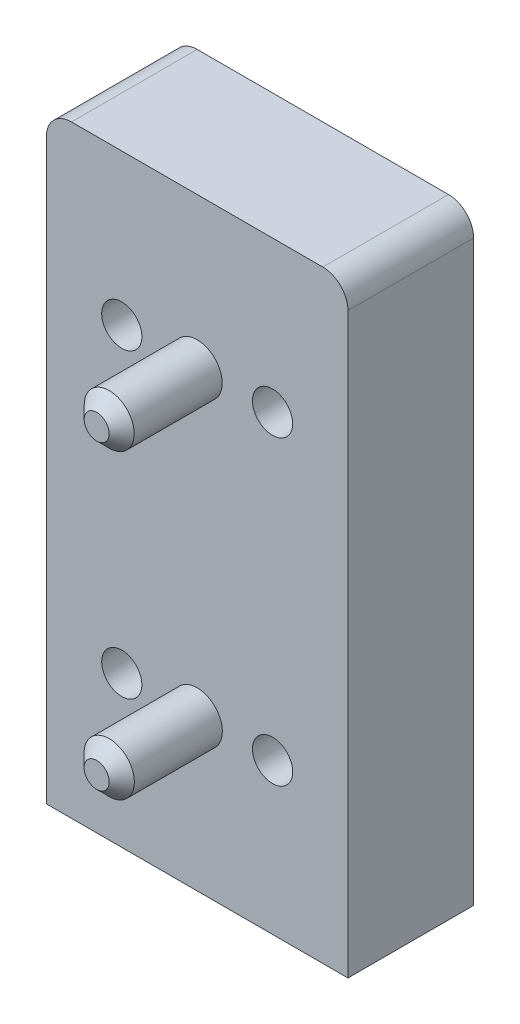
SolidWorks part; units mm, degrees
material "6061 Сплав"
ref_plane "Спереди" through (0, 0, 0) normal (0, 0, 1) x (1, 0, 0)
ref_plane "Сверху" through (0, 0, 0) normal (0, 1, 0) x (1, 0, 0)
ref_plane "Справа" through (0, 0, 0) normal (1, 0, 0) x (0, 0, -1)
sketch "Sketch1" plane through (0, 0, 0) normal (0, 0, 1) x (1, 0, 0)
  line L1 (-12, -36) -> (12, -36)
  line L2 (-12, -36) -> (-12, 10)
  line L3 (-10, 12) -> (10, 12)
  line L4 (12, -36) -> (12, 10)
  arc A0 (-12, 10) -> (-10, 12) centre (-10, 10) cw
  arc A1 (10, 12) -> (12, 10) centre (10, 10) cw
  point P0 (0, 0)
  point P10 (12, 12)
  dimension "D1" = 2
extrude "Boss-Extrude1" add sketch "Sketch1" along normal blind 10
sketch "Sketch2" plane through (0, 0, 0) normal (0, 0, -1) x (-1, 0, 0)
  line L0 (-1, -1.5) -> (1, -1.5)
  line L1 (-1.5, -1) -> (-1.5, 1)
  line L2 (-1, 1.5) -> (1, 1.5)
  line L3 (1.5, -1) -> (1.5, 1)
  line L4 (-1.5, -1.5) -> (1.5, 1.5) construction
  line L5 (-1.5, 1.5) -> (1.5, -1.5) construction
  line L6 (-1.76, -26.26) -> (1.76, -26.26)
  line L7 (-2.26, -25.76) -> (-2.26, -22.24)
  line L8 (-1.76, -21.74) -> (1.76, -21.74)
  line L9 (2.26, -25.76) -> (2.26, -22.24)
  line L10 (-2.26, -26.26) -> (2.26, -21.74) construction
  line L11 (-2.26, -21.74) -> (2.26, -26.26) construction
  circle A0 centre (4, -8) radius 1
  arc A1 (1.5, 1) -> (1, 1.5) centre (1.5, 1.5) ccw
  arc A2 (-1, 1.5) -> (-1.5, 1) centre (-1.5, 1.5) ccw
  arc A3 (1, -1.5) -> (1.5, -1) centre (1.5, -1.5) ccw
  arc A4 (-1.5, -1) -> (-1, -1.5) centre (-1.5, -1.5) ccw
  circle A5 centre (-0.116, -14.973) radius 1
  arc A6 (2.26, -22.24) -> (1.76, -21.74) centre (2.26, -21.74) ccw
  arc A7 (-1.76, -21.74) -> (-2.26, -22.24) centre (-2.26, -21.74) ccw
  arc A8 (-2.26, -25.76) -> (-1.76, -26.26) centre (-2.26, -26.26) ccw
  arc A9 (1.76, -26.26) -> (2.26, -25.76) centre (2.26, -26.26) ccw
  point P0 (0, 0)
  point P1 (0, 0)
  point P6 (-0.5312, 0.5468)
  point P7 (-0.5312, 0.5468)
  point P10 (7.5, 9)
  point P11 (-6.5, -8)
  point P12 (-6.5, 9)
  point P13 (7.5, -8)
  point P27 (0, -24)
  point P28 (0, -24)
  point P34 (6.884, -14.975)
  point P35 (-7.116, -14.973)
  point P36 (-7.116, -31.973)
  point P37 (6.884, -31.973)
  dimension "D11" = 3
  dimension "D24" = 0.5
  dimension "D1" = 9
  dimension "D2" = 8
  dimension "D3" = 6.5
  dimension "D4" = 7.5
  dimension "D5" = 8
  dimension "D6" = 9
  dimension "D7" = 6.5
  dimension "D8" = 7.5
  dimension "D9" = 3.5
  dimension "D10" = 8
  dimension "D12" = 3
  dimension "D13" = 7.116
  dimension "D14" = 6.884
  dimension "D15" = 9.025
  dimension "D16" = 7.973
  dimension "D17" = 6.884
  dimension "D18" = 7.116
  dimension "D19" = 7.973
  dimension "D20" = 9.027
  dimension "D21" = 7
  dimension "D22" = 4.52
  dimension "D23" = 4.52
  dimension "D25" = 9.027
extrude "Cut-Extrude1" cut sketch "Sketch2" against normal blind 0.6
sketch "Sketch3" plane through (0, 0, 10) normal (0, 0, 1) x (1, 0, 0)
  circle A0 centre (0, 0) radius 1.99
  circle A1 centre (0, -24) radius 2
extrude "Boss-Extrude3" add sketch "Sketch3" along normal blind 8
sketch "Sketch6" plane through (0, 0, 0) normal (0, 0, -1) x (-1, 0, 0)
  point P0 (6, 0)
  point P1 (-6, 0)
chamfer "Chamfer3" distance 1 angle 45 2 edges at (1.99, 0, 18) (2, -24, 18)
hole_wizard "Зенковка для  винта с полупотайной головкой M31" positions "Sketch11" profile "Sketch12" countersink size "M3" standard "Ansi Metric" end condition through all
sketch "Sketch11" plane through (0, 0, 0) normal (0, 0, -1) x (-1, 0, 0)
  point P0 (6, 0)
  point P3 (-6, 0)
  point P6 (-6, -24)
  point P8 (6, -24)
sketch "Sketch12" plane through (-6, 0, 0) normal (1, 0, 0) x (0, 1, 0)
  line L0 (0, 0) -> (0, 18)
  line L1 (0, 18) -> (1.6, 18)
  line L2 (1.6, 18) -> (1.6, 1.55)
  line L3 (1.6, 1.55) -> (3.15, 0)
  line L5 (3.15, 0) -> (0, 0)
  line L6 (-1.6, 1.55) -> (-3.15, 0) construction
  line L11 (0, -6.35) -> (0, 107.95) construction
  dimension "Диаметр сквозного отверстия" = 3.2
  dimension "Глубина сквозного отверстия" = 18
  dimension "Диаметр передней зенковки" = 6.3
  dimension "Угол передней зенковки" = 90
hole_wizard "Отверстие обработанное метчиком M3x0.51" positions "Эскиз2" profile "Эскиз1" tap size "M3x0.5" standard "Ansi Metric"
sketch "Эскиз2" plane through (0, 0, 0) normal (0, 0, -1) x (-1, 0, 0)
  point P0 (-6.5, -8)
  point P3 (-6.5, 9)
  point P6 (7.5, 9)
  point P9 (7.5, -8)
  point P12 (6.884, -14.975)
  point P15 (6.884, -31.973)
  point P18 (-7.116, -14.973)
  point P21 (-7.116, -31.973)
cosmetic thread "Отверстие резьбы6" parameters "D1"=5, "D2"=3
cosmetic thread "Отверстие резьбы7" parameters "D1"=5, "D2"=3
cosmetic thread "Отверстие резьбы8" parameters "D1"=5, "D2"=3
cosmetic thread "Отверстие резьбы9" parameters "D1"=5, "D2"=3
cosmetic thread "Отверстие резьбы10" parameters "D1"=5, "D2"=3
cosmetic thread "Отверстие резьбы11" parameters "D1"=5, "D2"=3
cosmetic thread "Отверстие резьбы12" parameters "D1"=5, "D2"=3
cosmetic thread "Отверстие резьбы13" parameters "D1"=5, "D2"=3
sketch "Эскиз1" plane through (6.5, -8, 0) normal (1, 0, 0) x (0, 1, 0)
  line L0 (0, 0) -> (0, 7.2511)
  line L1 (0, 7.2511) -> (1.25, 6.5)
  line L2 (1.25, 6.5) -> (1.25, 0)
  line L5 (1.25, 0) -> (0, 0)
  line L10 (0, 7.2511) -> (-1.25, 6.5) construction
  line L11 (0, -6.35) -> (0, 107.95) construction
  dimension "Диаметр сверла" = 2.5
  dimension "Глубина сверла" = 6.5
  dimension "Угол заточки сверла" = 118
